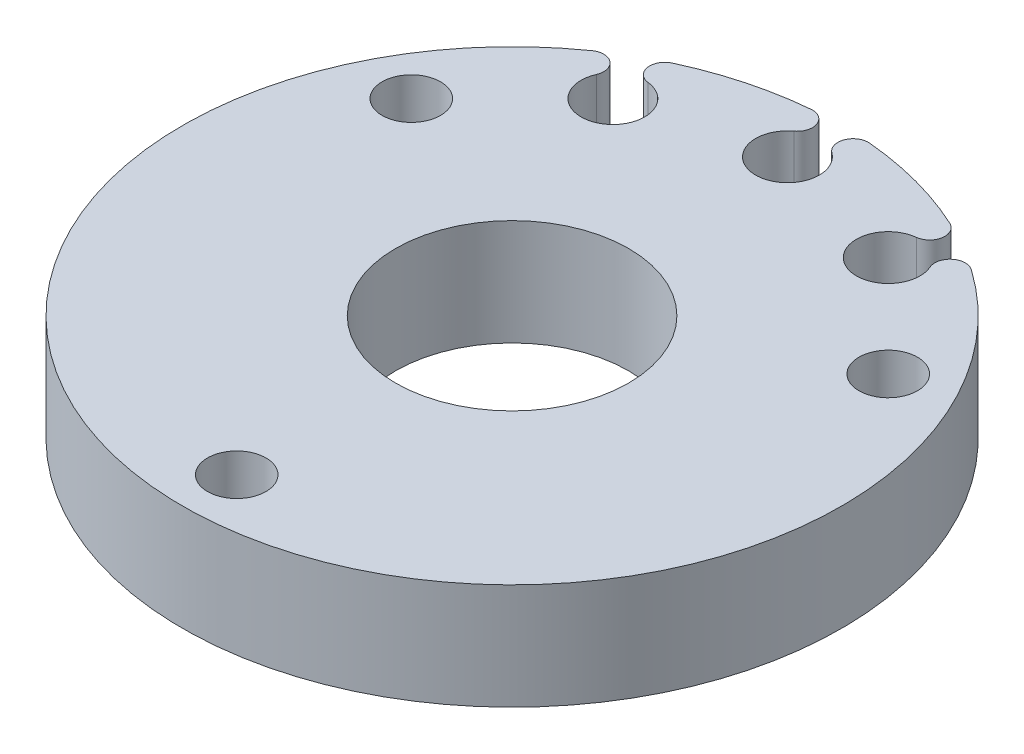
SolidWorks part; units mm, degrees
material "Cedar"
ref_plane "Front Plane" through (0, 0, 0) normal (0, 0, 1) x (1, 0, 0)
ref_plane "Top Plane" through (0, 0, 0) normal (0, 1, 0) x (1, 0, 0)
ref_plane "Right Plane" through (0, 0, 0) normal (1, 0, 0) x (0, 0, -1)
sketch "Sketch1" plane through (0, 0, 0) normal (0, 1, 0) x (1, 0, 0)
  line L0 (0, 16.5) -> (-14.2894, 8.25) construction
  line L1 (-14.2894, 8.25) -> (-14.2894, -8.25) construction
  circle A0 centre (0, 0) radius 19.75
  circle A1 centre (0, 0) radius 16.5 construction
  circle A2 centre (0, 0) radius 6.985
  circle A3 centre (0, 16.5) radius 1.75 construction
  circle A4 centre (-14.2894, 8.25) radius 1.75
  circle A5 centre (-14.2894, -8.25) radius 2.58 construction
  circle A6 centre (0, -16.5) radius 1.75
  circle A7 centre (14.2894, -8.25) radius 2.58 construction
  circle A8 centre (14.2894, 8.25) radius 1.75
  dimension "D1" = 39.5
  dimension "D2" = 33
  dimension "D3" = 13.97
  dimension "D4" = 3.5
  dimension "D5" = 5.16
extrude "Boss-Extrude1" add sketch "Sketch1" along normal blind 6.35
sketch "Sketch2" plane through (0, 6.35, 0) normal (0, 1, 0) x (1, 0, 0)
  line L0 (0, 0) -> (0, 11.1551) construction
  line L1 (7.1447, 12.375) -> (0, 0) construction
  line L2 (0, 0) -> (3.7596, 6.5118) construction
  arc A0 (8.0362, 16.1824) -> (9.9963, 15.0507) centre (8.25, 14.2894) ccw
  circle A1 centre (0, 0) radius 19.75 construction
  arc A2 (11.3546, 16.1597) -> (8.3174, 17.9132) centre (0, 0) ccw
  arc A3 (11.3546, 16.1597) -> (9.9963, 15.0507) centre (10.831, 15.4146) ccw
  arc A4 (8.3174, 17.9132) -> (8.0362, 16.1824) centre (7.9339, 17.0873) cw
  circle A5 centre (7.7822, 13.2861) radius 0.5207 construction
  circle A6 centre (7.4242, 14.8077) radius 0.6604 construction
  circle A7 centre (8.9696, 15.2328) radius 0.6604 construction
  circle A8 centre (9.1903, 13.6875) radius 0.5207 construction
  dimension "D2" = 3.81
  dimension "D5" = 1.0414
  dimension "D3" = 1.524
  dimension "D4" = 1.3208
  dimension "D1" = 16.5
  dimension "D6" = 30
extrude "Cut-Extrude1" cut sketch "Sketch2" against normal through all
pattern_circular "CirPattern1" count 3 every 30 about axis through (0, 0, 0) along (0, 1, 0) of "Cut-Extrude1"
